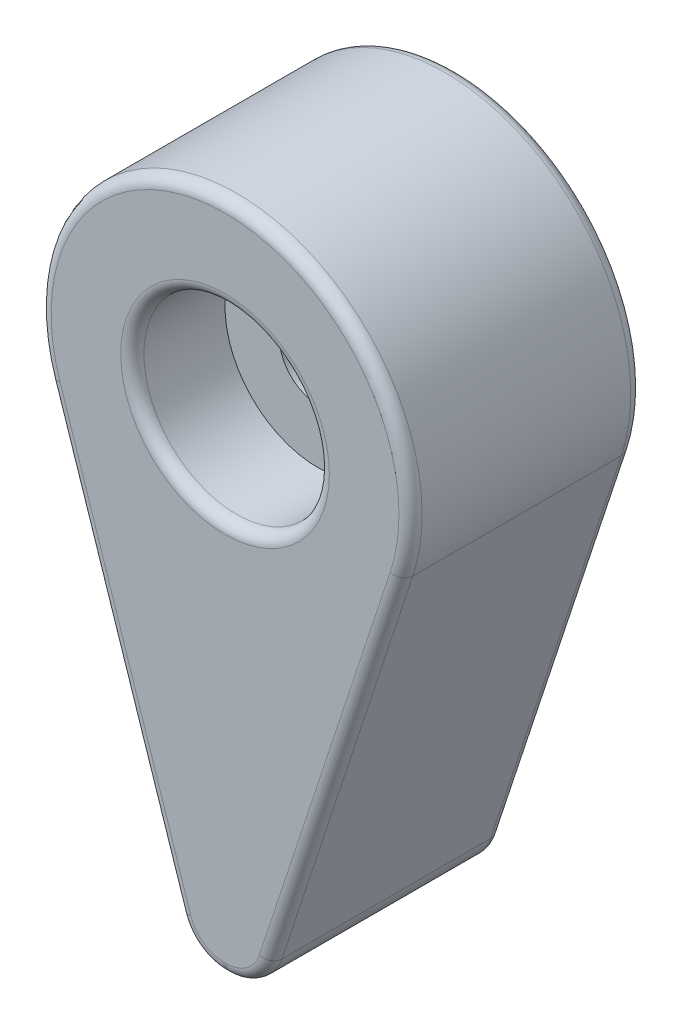
SolidWorks part; units mm, degrees
material "Сплав 2024"
ref_plane "Спереди" through (0, 0, 0) normal (0, 0, 1) x (1, 0, 0)
ref_plane "Сверху" through (0, 0, 0) normal (0, 1, 0) x (1, 0, 0)
ref_plane "Справа" through (0, 0, 0) normal (1, 0, 0) x (0, 0, -1)
sketch "Эскиз1" plane through (0, 0, 0) normal (0, 0, 1) x (1, 0, 0)
  line L0 (0, 18.3103) -> (0, -37.454) construction
  line L1 (-1.5, -21) -> (-7.5977, -2.5049)
  line L2 (1.5, -21) -> (7.5977, -2.5049)
  line L4 (-1.5, -21) -> (1.5, -21)
  arc A0 (7.5977, -2.5049) -> (-7.5977, -2.5049) centre (0, 0) ccw
  point P1 (0, -21)
  dimension "D1" = 16
  dimension "D2" = 3
  dimension "D3" = 21
extrude "Бобышка-Вытянуть1" add sketch "Эскиз1" along normal blind 10
hole_wizard "Цековка для винта с внутренним шестигранником M41" [suppressed] positions "Эскиз3" profile "Эскиз2" counterbore size "M4" standard "Ansi Metric"
sketch "Эскиз3" plane through (0, 10, 0) normal (0, 1, 0) x (1, 0, 0)
  point P0 (0, 0)
sketch "Эскиз2" plane through (0, 10, 0) normal (1, 0, 0) x (0, 0, 1)
  line L0 (0, 0) -> (0, 10)
  line L1 (0, 10) -> (2.25, 10)
  line L3 (2.25, 10) -> (2.25, 4)
  line L4 (2.25, 4) -> (4, 4)
  line L5 (4, 4) -> (4, 0)
  line L7 (4, 0) -> (0, 0)
  line L11 (0, -6.35) -> (0, 107.95) construction
  dimension "Диаметр сквозного отверстия" = 4.5
  dimension "Глубина сквозного отверстия" = 10
  dimension "Диаметр цековки" = 8
  dimension "Глубина цековки" = 4
fillet "Скругление1" radius 2 2 edges at (1.5, -21, 5) (-1.5, -21, 5)
fillet "Скругление2" [suppressed] radius 5
chamfer "Фаска1" [suppressed] distance 0.5 angle 45
sketch "Эскиз4" plane through (0, 0, 10) normal (0, 0, 1) x (1, 0, 0)
  circle A0 centre (0, 0) radius 4
  dimension "D1" = 8
extrude "Вырез-Вытянуть1" cut sketch "Эскиз4" against normal blind 4
hole_wizard "Отверстие обработанное метчиком M4x0.71" positions "Эскиз6" profile "Эскиз5" tap size "M4x0.7" standard "Ansi Metric" end condition through all
sketch "Эскиз6" plane through (0, 0, 6) normal (0, 0, 1) x (1, 0, 0)
  point P0 (0, 0)
sketch "Эскиз5" plane through (0, 0, 6) normal (1, 0, 0) x (0, -1, 0)
  line L0 (0, 0) -> (0, 6)
  line L1 (0, 6) -> (1.65, 6)
  line L2 (1.65, 6) -> (1.65, 0)
  line L5 (1.65, 0) -> (0, 0)
  line L11 (0, -6.35) -> (0, 107.95) construction
  dimension "Диаметр проходного сверла" = 3.3
  dimension "Глубина проходного сверла" = 6
cosmetic thread "Отверстие резьбы1" parameters "D2"=4
fillet "Скругление3" radius 0.5 14 edges at (0, 8, 0) (-4.7753, -11.0656, 0) (-1.2256, -20.6206, 0) (0, -21, 0) (1.2256, -20.6206, 0) (4.7753, -11.0656, 0) (1.65, 0, 0) (-1.2256, -20.6206, 10) (-4.7753, -11.0656, 10) (0, 8, 10) (4.7753, -11.0656, 10) (1.2256, -20.6206, 10) (0, -21, 10) (4, 0, 10)
